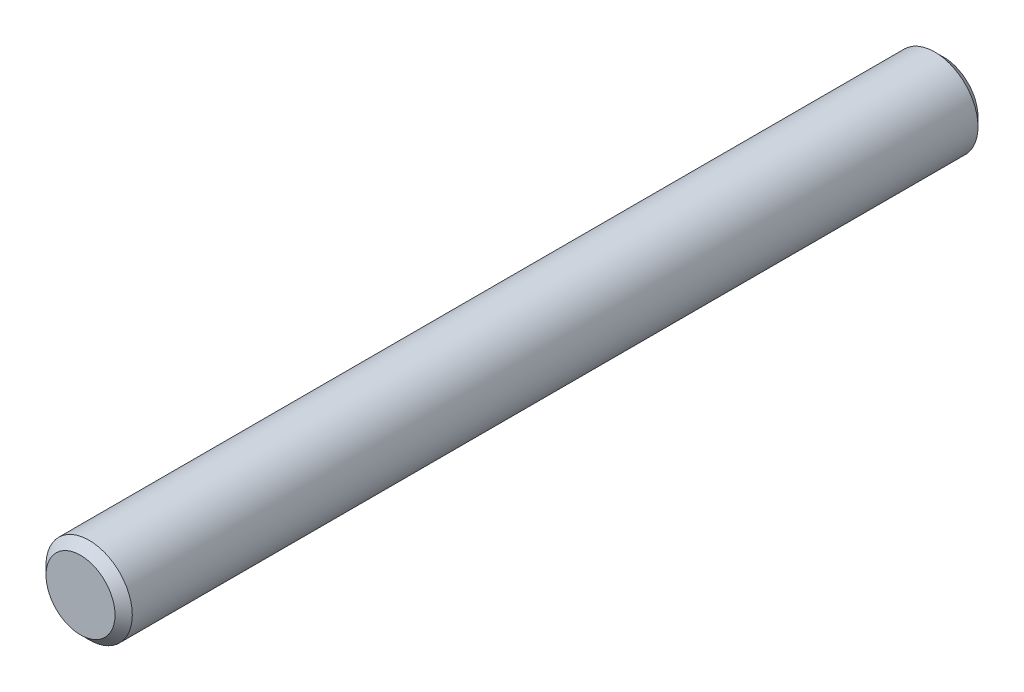
SolidWorks part; units mm, degrees
ref_plane "前视基准面" through (0, 0, 0) normal (0, 0, 1) x (1, 0, 0)
ref_plane "上视基准面" through (0, 0, 0) normal (0, 1, 0) x (1, 0, 0)
ref_plane "右视基准面" through (0, 0, 0) normal (1, 0, 0) x (0, 0, -1)
sketch "草图1" plane through (0, 0, 0) normal (0, 0, 1) x (1, 0, 0)
  circle A0 centre (0, 0) radius 1
  dimension "D1" = 2
extrude "凸台-拉伸1" add sketch "草图1" along normal mid plane 20
chamfer "倒角1" distance 0.2 angle 45 2 edges at (1, 0, -10) (1, 0, 10)
